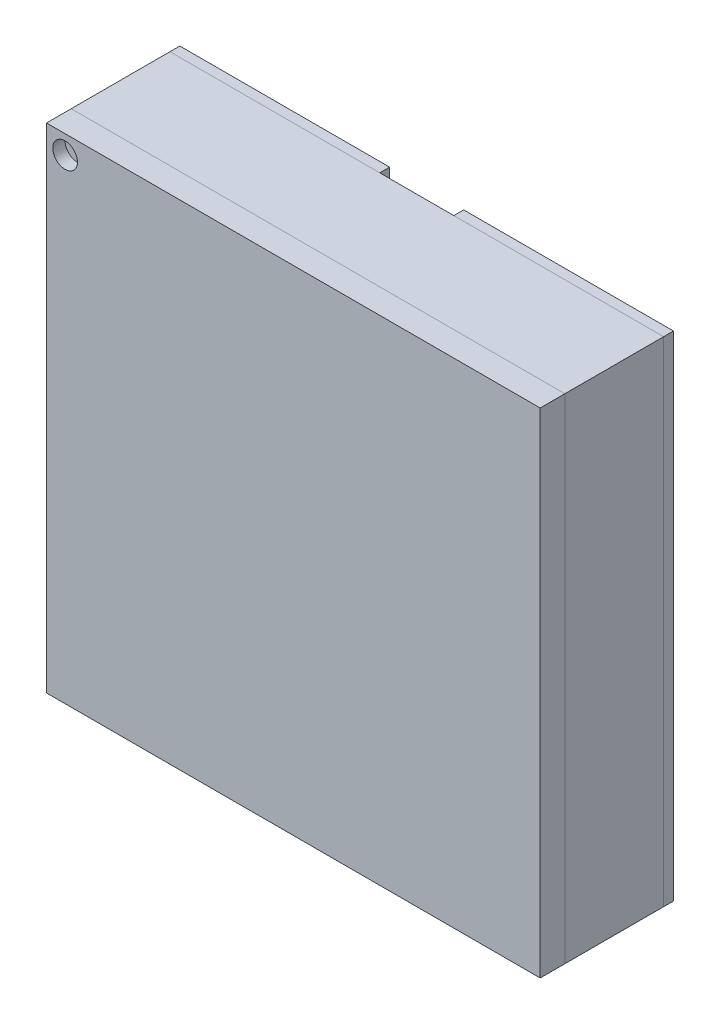
SolidWorks part; units mm, degrees
ref_plane "Ebene vorne" through (0, 0, 0) normal (0, 0, 1) x (1, 0, 0)
ref_plane "Ebene oben" through (0, 0, 0) normal (0, 1, 0) x (1, 0, 0)
ref_plane "Ebene rechts" through (0, 0, 0) normal (1, 0, 0) x (0, 0, -1)
sketch "Model" plane through (0, 0, 0) normal (0, 0, 1) x (1, 0, 0)
  line L0 (10.705, 89.295) -> (12.705, 89.295)
  line L1 (12.705, 89.295) -> (12.705, 87.295)
  line L2 (12.705, 87.295) -> (10.705, 87.295)
  line L3 (10.705, 87.295) -> (10.705, 89.295)
extrude "Boss-Extrude1" add sketch "Model" along normal blind 0.4
sketch "Sketch2" plane through (0, 0, 0) normal (0, 0, -1) x (-1, 0, 0)
  line L0 (-11.705, 89.295) -> (-11.705, 87.295) construction
  line L1 (-12.705, 89.295) -> (-10.705, 89.295) construction
  line L2 (-10.705, 87.295) -> (-12.705, 87.295) construction
  line L4 (-11.855, 89.295) -> (-11.555, 89.295)
  line L5 (-11.855, 89.295) -> (-11.855, 87.295)
  line L6 (-11.855, 87.295) -> (-11.555, 87.295)
  line L7 (-11.555, 89.295) -> (-11.555, 87.295)
  line L8 (-11.855, 89.295) -> (-11.555, 87.295) construction
  line L9 (-11.855, 87.295) -> (-11.555, 89.295) construction
  line L10 (-11.855, 87.295) -> (-12.705, 87.295)
  line L11 (-11.855, 87.295) -> (-11.855, 89.295)
  line L12 (-11.855, 89.295) -> (-12.705, 89.295)
  line L13 (-12.705, 87.295) -> (-12.705, 89.295)
  line L14 (-11.555, 87.295) -> (-10.705, 87.295)
  line L15 (-11.555, 87.295) -> (-11.555, 89.295)
  line L16 (-11.555, 89.295) -> (-10.705, 89.295)
  line L17 (-10.705, 87.295) -> (-10.705, 89.295)
  point P6 (-11.705, 88.295)
  line M5 (-10.705, 87.295) -> (-10.705, 89.295)
  line M6 (-10.705, 89.295) -> (-12.705, 89.295)
  line M7 (-12.705, 89.295) -> (-12.705, 87.295)
  line M8 (-12.705, 87.295) -> (-10.705, 87.295)
  dimension "D1" = 0.3
sketch "Sketch3" plane through (0, 0, 0.4) normal (0, 0, 1) x (1, 0, 0)
  line L4 (10.705, 89.295) -> (10.705, 87.295)
  line L5 (10.705, 87.295) -> (12.705, 87.295)
  line L6 (12.705, 87.295) -> (12.705, 89.295)
  line L7 (12.705, 89.295) -> (10.705, 89.295)
  line L8 (10.705, 89.295) -> (10.705, 87.295)
  line L9 (10.705, 87.295) -> (12.705, 87.295)
  line L10 (12.705, 87.295) -> (12.705, 89.295)
  line L11 (12.705, 89.295) -> (10.705, 89.295)
  dimension "D1" = 0
extrude "Boss-Extrude2" add sketch "Sketch3" along normal blind 0.1 separate body
extrude "Boss-Extrude3" add sketch "Sketch2" along normal blind 0.04 separate body contours L7 M6 M8 M5 | L5 M6 M7 M8
sketch "Sketch4" plane through (0, 0, 0.5) normal (0, 0, 1) x (1, 0, 0)
  line L2 (10.705, 89.295) -> (12.705, 87.295) construction
  circle A0 centre (10.7803, 89.2197) radius 0.05
  dimension "D1" = 0.1
extrude "Cut-Extrude1" cut sketch "Sketch4" against normal blind 0.05
sketch "Sketch6" plane through (0, 0, -0.04) normal (0, 0, -1) x (-1, 0, 0)
  line L0 (-12.28, 89.295) -> (-12.28, 87.295) construction
  line L1 (-11.855, 89.295) -> (-12.705, 89.295) construction
  line L2 (-12.705, 87.295) -> (-11.855, 87.295) construction
  line L3 (-11.705, 89.295) -> (-11.705, 87.295) construction
  line L4 (-12.705, 89.295) -> (-10.705, 89.295) construction
  line L5 (-10.705, 87.295) -> (-12.705, 87.295) construction
  circle A0 centre (-12.28, 88.895) radius 0.2
  circle A1 centre (-11.13, 88.895) radius 0.2
  dimension "D1" = 0.4
  dimension "D2" = 0.4
extrude "Cut-Extrude3" cut sketch "Sketch6" against normal blind 0.02
sketch "Sketch5" plane through (0, 0, -0.04) normal (0, 0, -1) x (-1, 0, 0)
  line L0 (-10.8464, 89.295) -> (-10.705, 89.1536)
  line L1 (-10.705, 89.295) -> (-11.555, 89.295) construction
  line L2 (-10.705, 87.295) -> (-10.705, 89.295) construction
  line L3 (-10.8464, 89.295) -> (-10.705, 89.295)
  line L4 (-10.705, 89.295) -> (-10.705, 89.1536)
  dimension "D1" = 45
  dimension "D2" = 0.2
extrude "Cut-Extrude2" [suppressed] cut sketch "Sketch5" against normal blind 0.04
